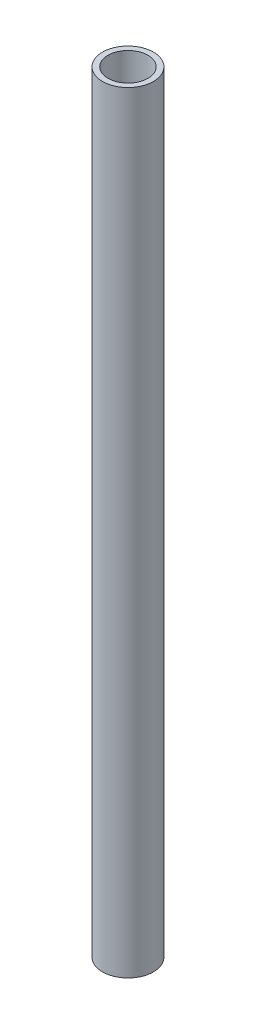
SolidWorks part; units mm, degrees
ref_plane "Front Plane" through (0, 0, 0) normal (0, 0, 1) x (1, 0, 0)
ref_plane "Top Plane" through (0, 0, 0) normal (0, 1, 0) x (1, 0, 0)
ref_plane "Right Plane" through (0, 0, 0) normal (1, 0, 0) x (0, 0, -1)
sketch "Sketch1" plane through (0, 0, 0) normal (0, 1, 0) x (1, 0, 0)
  circle A0 centre (0, 0) radius 16.764
  circle A1 centre (0, 0) radius 13.1762
  dimension "D1" = 33.528
  dimension "D2" = 26.3525
extrude "Boss-Extrude1" add sketch "Sketch1" along normal blind 508
